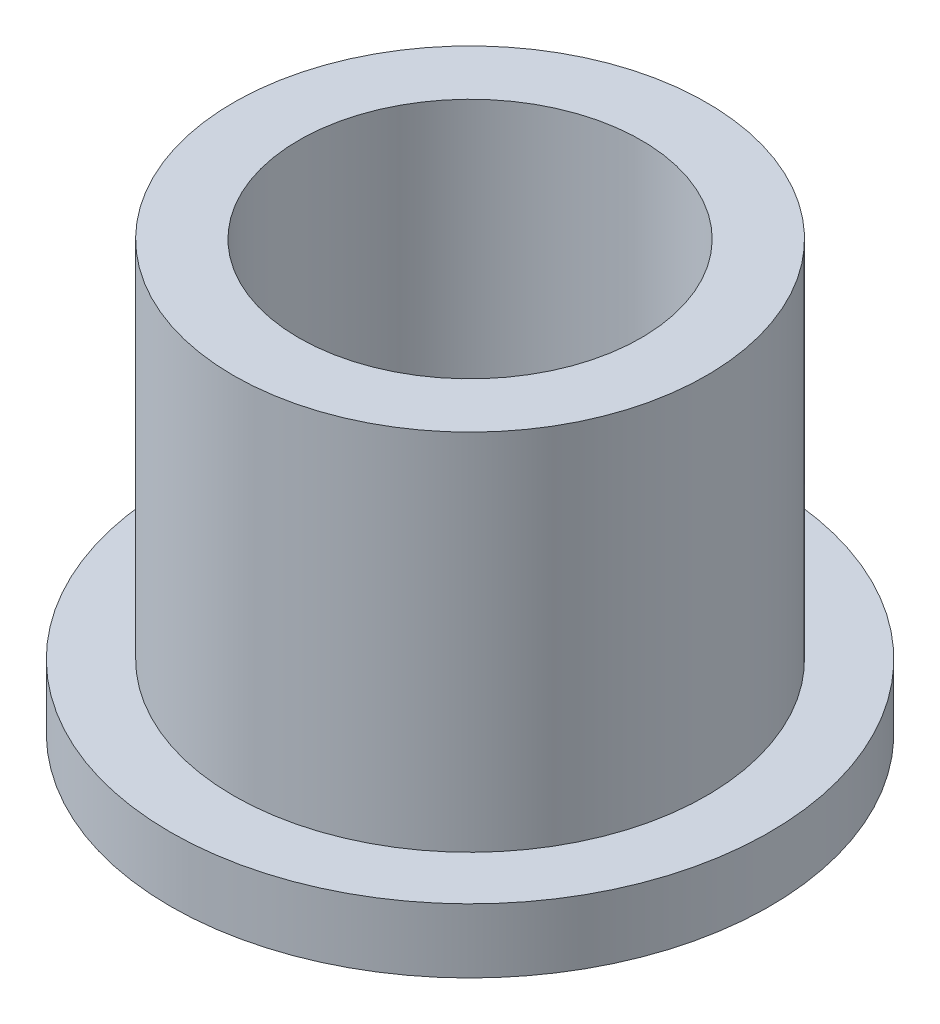
SolidWorks part; units mm, degrees
material "Brass"
ref_plane "Front" through (0, 0, 0) normal (0, 0, 1) x (1, 0, 0)
ref_plane "Top" through (0, 0, 0) normal (0, 1, 0) x (1, 0, 0)
ref_plane "Right" through (0, 0, 0) normal (1, 0, 0) x (0, 0, -1)
sketch "Sketch1" plane through (0, 0, 0) normal (0, 1, 0) x (1, 0, 0)
  circle A0 centre (0, 0) radius 4
  circle A1 centre (0, 0) radius 5.525
  circle A2 centre (0, 0) radius 7
  dimension "ID" = 8
  dimension "OD" = 11.05
  dimension "FlangeOD" = 14
sketch "Sketch2" plane through (0, 0, 0) normal (0, 1, 0) x (1, 0, 0)
  circle A0 centre (0, 0) radius 4 construction
  circle A1 centre (0, 0) radius 5.525 construction
  circle A2 centre (0, 0) radius 4
  circle A3 centre (0, 0) radius 5.525
extrude "Boss-Extrude1" add sketch "Sketch2" along normal blind 10
sketch "Sketch3" plane through (0, 0, 0) normal (0, 1, 0) x (1, 0, 0)
  circle A0 centre (0, 0) radius 7 construction
  circle A1 centre (0, 0) radius 5.525 construction
  circle A2 centre (0, 0) radius 7
  circle A3 centre (0, 0) radius 5.525
extrude "Boss-Extrude2" add sketch "Sketch3" along normal blind 1.5
